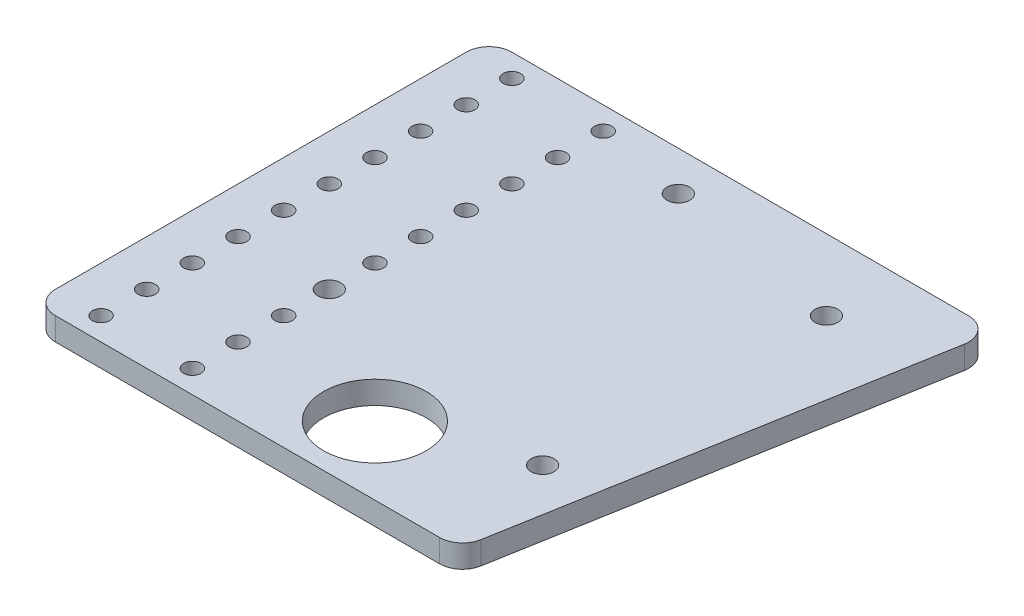
SolidWorks part; units mm, degrees
material "1023 Carbon Steel Sheet (SS)"
ref_plane "Front Plane" through (0, 0, 0) normal (0, 0, 1) x (1, 0, 0)
ref_plane "Top Plane" through (0, 0, 0) normal (0, 1, 0) x (1, 0, 0)
ref_plane "Right Plane" through (0, 0, 0) normal (1, 0, 0) x (0, 0, -1)
sketch "Sketch1" plane through (0, 0, 0) normal (0, 1, 0) x (1, 0, 0)
  line L1 (-64.4036, -58.0213) -> (54.1729, -58.0213)
  line L2 (-64.4036, -58.0213) -> (-64.4036, 68.9787)
  line L3 (-64.4036, 68.9787) -> (76.5664, 68.9787)
  line L4 (54.1729, -58.0213) -> (76.5664, 68.9787)
  line L5 (-64.4036, -58.0213) -> (76.5664, 68.9787) construction
  line L6 (-64.4036, 68.9787) -> (54.1729, -58.0213) construction
  point P0 (0, 0)
  dimension "D1" = 127
  dimension "D2" = 140.97
  dimension "D4" = 80
extrude "Initial Plate" add sketch "Sketch1" along normal blind 6.35
sketch "Sketch3" plane through (0, 6.35, 0) normal (0, 1, 0) x (1, 0, 0)
  line L0 (51.7036, -51.6713) -> (-51.7036, -51.6713) construction
  line L1 (0, 0) -> (0, -51.6713) construction
  line L2 (-64.4036, -58.0213) -> (54.1729, -58.0213) construction
  line L3 (-64.4036, 68.9787) -> (-64.4036, -58.0213) construction
  circle A0 centre (-51.7036, -51.6713) radius 2.413
  circle A1 centre (51.7036, -51.6713) radius 2.413 construction
  circle A2 centre (-26.3036, -51.6713) radius 2.413
  point P4 (0, 0)
  dimension "D1" = 4.826
  dimension "D2" = 6.35
  dimension "D3" = 12.7
  dimension "D4" = 25.4
extrude "Initial Mounting Hole" cut sketch "Sketch3" against normal through all
pattern_linear "Mounting Pattern" count 10 spacing 12.7 along (0, 0, -1) of "Initial Mounting Hole"
sketch "Sketch2" plane through (0, 6.35, 0) normal (0, 1, 0) x (1, 0, 0)
  line L0 (42.7374, 12.2979) -> (-19.7979, 23.3246) construction
  line L1 (-26.3036, -13.5713) -> (-13.2921, 60.2204) construction
  line L2 (36.2317, -24.5979) -> (49.2432, 49.1937) construction
  line L3 (-64.4036, -58.0213) -> (54.1729, -58.0213) construction
  line L4 (-26.7654, 56.1481) -> (-37.2169, 57.991) construction
  line L5 (-16.9839, -8.7666) -> (-27.4353, -6.9237) construction
  line L6 (-13.2921, 60.2204) -> (-0.7851, 58.0151) construction
  line L7 (36.2317, -24.5979) -> (45.7371, -26.274) construction
  circle A1 centre (-26.3036, -13.5713) radius 3.175
  circle A3 centre (49.2432, 49.1937) radius 3.175
  circle A5 centre (-26.3036, -13.5713) radius 6.35 construction
  circle A6 centre (45.7371, -26.274) radius 3.175
  circle A7 centre (-26.3036, -13.5713) radius 2.413 construction
  circle A10 centre (-0.7851, 58.0151) radius 3.175
  circle A11 centre (-0.7851, 58.0151) radius 6.35 construction
  point P4 (1.7785, 19.5201)
  point P7 (-19.7979, 23.3246)
  point P10 (42.7374, 12.2979)
  dimension "D5" = 6.35
  dimension "D2" = 12.7
  dimension "D1" = 63.5
  dimension "D4" = 10
  dimension "D6" = 62.23
  dimension "D8" = 0
  dimension "D3" = 12.7
  dimension "D7" = 9.652
extrude "Bearing Stack Holes" cut sketch "Sketch2" against normal through all
fillet "Fillet1" radius 6.35 4 edges at (76.5664, 3.175, -68.9787) (54.1729, 3.175, 58.0213) (-64.4036, 3.175, 58.0213) (-64.4036, 3.175, -68.9787)
sketch "Sketch4" plane through (0, 6.35, 0) normal (0, 1, 0) x (1, 0, 0)
  circle A0 centre (11.7926, -38.9775) radius 14.2875
  dimension "D1" = 28.575
extrude "Cut-Extrude1" cut sketch "Sketch4" against normal through all
mirror "Mirror1" [suppressed] about plane through (0, 0, 0) normal (1, 0, 0)
delete or keep bodies "Body-Delete/Keep 1" [suppressed] type delete bodies bodies 105
equation "\"D6@Sketch2\"= 2.5in - 0.05in"
